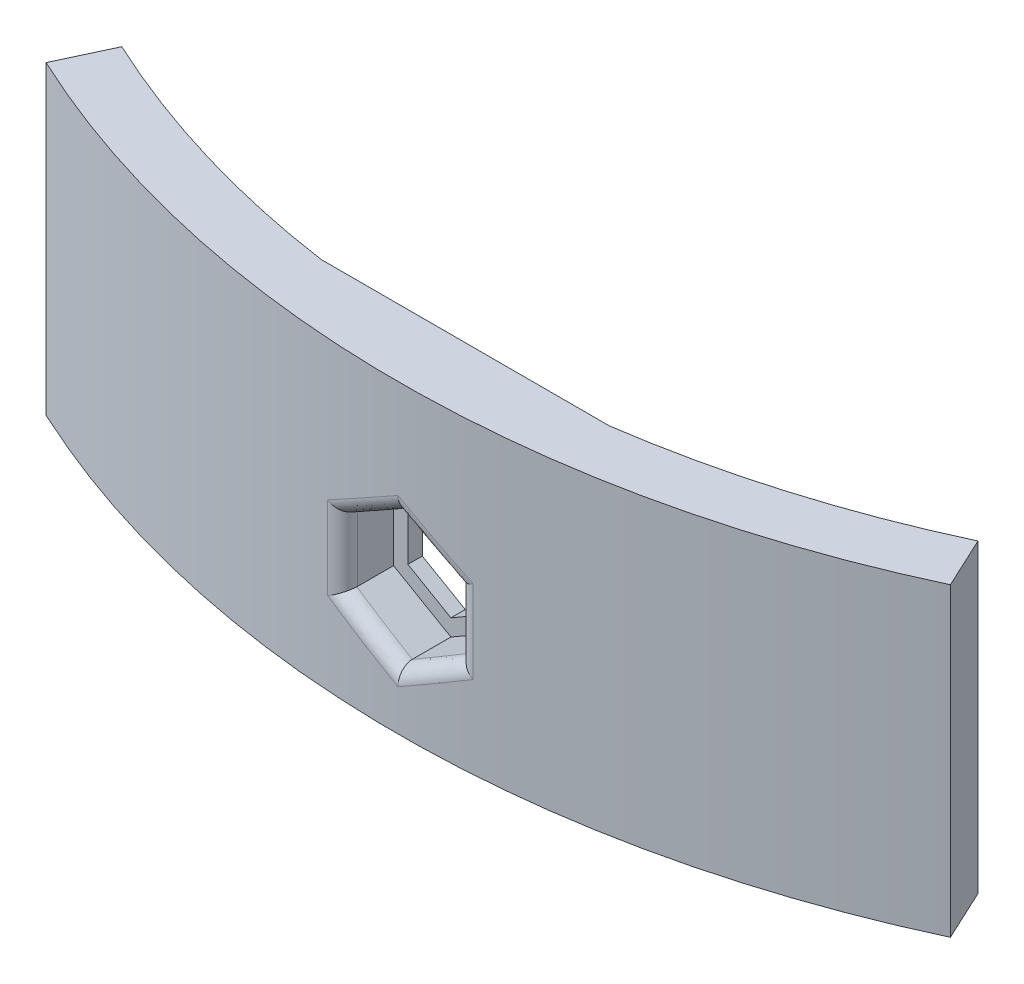
SolidWorks part; units mm, degrees
ref_plane "Front Plane" through (0, 0, 0) normal (0, 0, 1) x (1, 0, 0)
ref_plane "Top Plane" through (0, 0, 0) normal (0, 1, 0) x (1, 0, 0)
ref_plane "Right Plane" through (0, 0, 0) normal (1, 0, 0) x (0, 0, -1)
sketch "Sketch1" plane through (0, 0, 0) normal (0, 0, 1) x (1, 0, 0)
  line L1 (0, 5.842) -> (-5.0593, 2.921)
  line L2 (-5.0593, 2.921) -> (-5.0593, -2.921)
  line L3 (-5.0593, -2.921) -> (0, -5.842)
  line L4 (0, -5.842) -> (5.0593, -2.921)
  line L5 (5.0593, -2.921) -> (5.0593, 2.921)
  line L6 (5.0593, 2.921) -> (0, 5.842)
  line L7 (-12.7, -10.922) -> (12.7, -10.922)
  line L8 (-12.7, -10.922) -> (-12.7, 10.922)
  line L9 (-12.7, 10.922) -> (12.7, 10.922)
  line L10 (12.7, -10.922) -> (12.7, 10.922)
  line L11 (-12.7, -10.922) -> (12.7, 10.922) construction
  line L12 (-12.7, 10.922) -> (12.7, -10.922) construction
  circle A0 centre (0, 0) radius 5.0593 construction
  dimension "D2" = 11.684
  dimension "D1" = 25.4
  dimension "D3" = 5.08
extrude "Bolt Size, Width, &Height" add sketch "Sketch1" along normal blind 7.62
sketch "Sketch2" plane through (0, 10.922, 0) normal (0, 1, 0) x (1, 0, 0)
  line L0 (-12.7, -7.62) -> (-12.7, 0) construction
  line L1 (12.7, -7.62) -> (12.7, 0) construction
  line L6 (12.7, 0) -> (-12.7, 0)
  line L7 (-12.7, 0) -> (-12.7, -7.62)
  line L8 (-12.7, -7.62) -> (12.7, -7.62)
  line L9 (12.7, -7.62) -> (12.7, 0)
  line L10 (12.7, 0) -> (-12.7, 0)
  line L11 (-12.7, 0) -> (-12.7, -7.62)
  line L12 (-12.7, -7.62) -> (12.7, -7.62)
  line L13 (12.7, -7.62) -> (12.7, 0)
  arc A0 (-12.7, -3.81) -> (12.7, -3.81) centre (0, 89.6925) ccw
  line M7 (-12.7, -7.62) -> (12.7, -7.62)
  line M8 (12.7, -7.62) -> (12.7, 0)
  dimension "D1" = 94.361
  dimension "D2" = 0
extrude "Front Curve" cut sketch "Sketch2" against normal through all contours A0 L11 M7 M8
sketch "Sketch3" plane through (0, 0, 0) normal (0, 0, -1) x (-1, 0, 0)
  line L0 (-12.7, -10.922) -> (-12.7, 10.922) construction
  line L1 (-12.7, -10.922) -> (-12.7, 10.922)
  line L2 (-12.7, 10.922) -> (12.7, 10.922) construction
  line L3 (-12.7, 10.922) -> (12.7, 10.922)
  line L4 (12.7, 10.922) -> (12.7, -10.922) construction
  line L5 (12.7, 10.922) -> (12.7, -10.922)
  line L6 (12.7, -10.922) -> (-12.7, -10.922) construction
  line L7 (12.7, -10.922) -> (-12.7, -10.922)
  line L35 (-3.7893, 2.1878) -> (-3.7893, -2.1878)
  line L36 (-3.7893, -2.1878) -> (0, -4.3755)
  line L37 (0, -4.3755) -> (3.7893, -2.1878)
  line L38 (3.7893, -2.1878) -> (3.7893, 2.1878)
  line L39 (3.7893, 2.1878) -> (0, 4.3755)
  line L40 (0, 4.3755) -> (-3.7893, 2.1878)
  line L41 (-3.7893, 2.1878) -> (-3.7893, -2.1878)
  line L42 (-3.7893, -2.1878) -> (0, -4.3755)
  line L43 (0, -4.3755) -> (3.7893, -2.1878)
  line L44 (3.7893, -2.1878) -> (3.7893, 2.1878)
  line L45 (3.7893, 2.1878) -> (0, 4.3755)
  line L46 (0, 4.3755) -> (-3.7893, 2.1878)
  dimension "D1" = 1.27
extrude "Rear Cap" add sketch "Sketch3" along normal blind 1.27
sketch "Sketch6" plane through (0, -10.922, 0) normal (0, -1, 0) x (1, 0, 0)
  line L0 (-39.8787, -4.1723) -> (-37.7524, -8.7321)
  line L1 (39.8787, -4.1723) -> (37.7524, -8.7321)
  line L2 (0, 4.6685) -> (0, -0.3626) construction
  line L3 (-12.7, 3.81) -> (-12.7, -1.27)
  line L4 (-12.7, -1.27) -> (12.7, -1.27)
  line L5 (12.7, -1.27) -> (12.7, 3.81)
  line L6 (-12.7, 3.81) -> (-12.7, -1.27)
  line L7 (-12.7, -1.27) -> (12.7, -1.27)
  line L8 (12.7, -1.27) -> (12.7, 3.81)
  circle A0 centre (0, -89.6925) radius 94.361
  circle A1 centre (0, -89.6925) radius 89.3298
  arc A2 (12.7, 3.81) -> (-12.7, 3.81) centre (0, -89.6925) ccw
  arc A3 (12.7, 3.81) -> (-12.7, 3.81) centre (0, -89.6925) ccw
  line M8 (-12.7, 3.81) -> (-12.7, -1.27)
  line M10 (12.7, -1.27) -> (12.7, 3.81)
  dimension "D2" = 25
  dimension "D3" = 25
  dimension "D1" = 0
extrude "Wings" add sketch "Sketch6" against normal up to surface (21.844 mm away) contours A1 A0 L0 M8 | A1 L1 A0 M10 up to face at (0, 10.922, 1.4846)
sketch "Sketch7" plane through (0, 10.922, 0) normal (0, 1, 0) x (1, 0, 0)
  line L1 (-12.7, 1.27) -> (12.7, 1.27) construction
  line L2 (-12.7, 1.27) -> (12.7, 1.27)
  line L3 (-37.7524, 8.7321) -> (-42.905, -2.3176)
  line L4 (37.7524, 8.7321) -> (42.905, -2.3176)
  line L5 (-19.05, -2.7256) -> (-20.4957, -9.739)
  line L6 (19.05, -2.7256) -> (20.4957, -9.739)
  circle A0 centre (0, 89.6925) radius 101.5218
  arc A1 (-39.8787, 4.1723) -> (39.8787, 4.1723) centre (0, 89.6925) ccw construction
  arc A2 (12.7, 1.27) -> (37.7524, 8.7321) centre (0, 89.6925) ccw construction
  arc A3 (-37.7524, 8.7321) -> (-12.7, 1.27) centre (0, 89.6925) ccw construction
  arc A4 (12.7, 1.27) -> (37.7524, 8.7321) centre (0, 89.6925) ccw
  arc A5 (-37.7524, 8.7321) -> (-12.7, 1.27) centre (0, 89.6925) ccw
  arc A6 (-39.8787, 4.1723) -> (39.8787, 4.1723) centre (0, 89.6925) ccw
  dimension "D1" = 12.192
  dimension "D2" = 38.1
  dimension "D3" = 19.05
extrude "Hook Depth" add sketch "Sketch7" along normal blind 5.08
sketch "Sketch8" plane through (0, 10.922, 0) normal (0, -1, 0) x (1, 0, 0)
  line L0 (0, 4.6685) -> (0, -1.27) construction
  line L1 (12.7, -1.27) -> (-12.7, -1.27) construction
  line L2 (-42.905, 2.3176) -> (-39.8787, -4.1723)
  line L3 (-19.05, 2.7256) -> (-20.4957, 9.739)
  line L4 (-42.905, 2.3176) -> (-39.8787, -4.1723)
  line L5 (-19.05, 2.7256) -> (-20.4957, 9.739)
  line L6 (42.905, 2.3176) -> (39.8787, -4.1723)
  line L7 (19.05, 2.7256) -> (20.4957, 9.739)
  arc A0 (-41.8315, 0.0156) -> (-19.9829, 7.2513) centre (0, -89.6925) cw
  arc A1 (19.05, 2.7256) -> (39.8787, -4.1723) centre (0, -89.6925) cw
  arc A2 (-19.05, 2.7256) -> (-39.8787, -4.1723) centre (0, -89.6925) ccw
  arc A3 (-20.4957, 9.739) -> (-42.905, 2.3176) centre (0, -89.6925) ccw
  arc A4 (-19.05, 2.7256) -> (-39.8787, -4.1723) centre (0, -89.6925) ccw
  arc A5 (-20.4957, 9.739) -> (-42.905, 2.3176) centre (0, -89.6925) ccw
  arc A6 (20.4957, 9.739) -> (42.905, 2.3176) centre (0, -89.6925) cw
  arc A7 (41.8315, 0.0156) -> (19.9829, 7.2513) centre (0, -89.6925) ccw
  line M6 (-42.905, 2.3176) -> (-39.8787, -4.1723)
  arc M9 (-20.4957, 9.739) -> (-42.905, 2.3176) centre (0, -89.6925) ccw
  dimension "D2" = 2.54
  dimension "D3" = 2.54
  dimension "D1" = 0
extrude "Hook Height" add sketch "Sketch8" along normal blind 3.81 contours A0 L5 M6 M9 | A7 L6 A6 L7
fillet "Nut Flange Clearance" radius 1.27 6 edges at (-2.5306, -4.381, 4.6346) (2.5306, -4.381, 4.6346) (5.0593, 0, 4.5328) (2.5306, 4.381, 4.6346) (-2.5306, 4.381, 4.6346) (-5.0593, 0, 4.5328)
chamfer "Decoration" distance 2.54 angle 45 4 edges at (20.2393, 7.112, 8.4951) (42.3683, 7.112, 1.1666) (-42.3683, 7.112, 1.1666) (-20.2393, 7.112, 8.4951)
sketch "Sketch9" plane through (0, 16.002, 0) normal (0, 1, 0) x (1, 0, 0)
  line L0 (-37.7524, 8.7321) -> (-42.905, -2.3176) construction
  line L1 (42.905, -2.3176) -> (39.8787, 4.1723)
  line L2 (-39.8787, 4.1723) -> (-42.905, -2.3176)
  arc A1 (39.8787, 4.1723) -> (-39.8787, 4.1723) centre (0, 89.6925) cw
  arc A3 (-42.905, -2.3176) -> (42.905, -2.3176) centre (0, 89.6925) ccw
  arc A4 (20.4957, -9.739) -> (42.905, -2.3176) centre (0, 89.6925) ccw construction
  arc A5 (19.05, -2.7256) -> (39.8787, 4.1723) centre (0, 89.6925) ccw construction
  arc A6 (19.05, -2.7256) -> (39.8787, 4.1723) centre (0, 89.6925) ccw construction
extrude "Cut-Extrude1" cut sketch "Sketch9" against normal through all
equation "\"D3@Sketch6\"=\"D2@Sketch6\""
equation "\"D3@Sketch7\"=\"D2@Sketch7\"/2"
